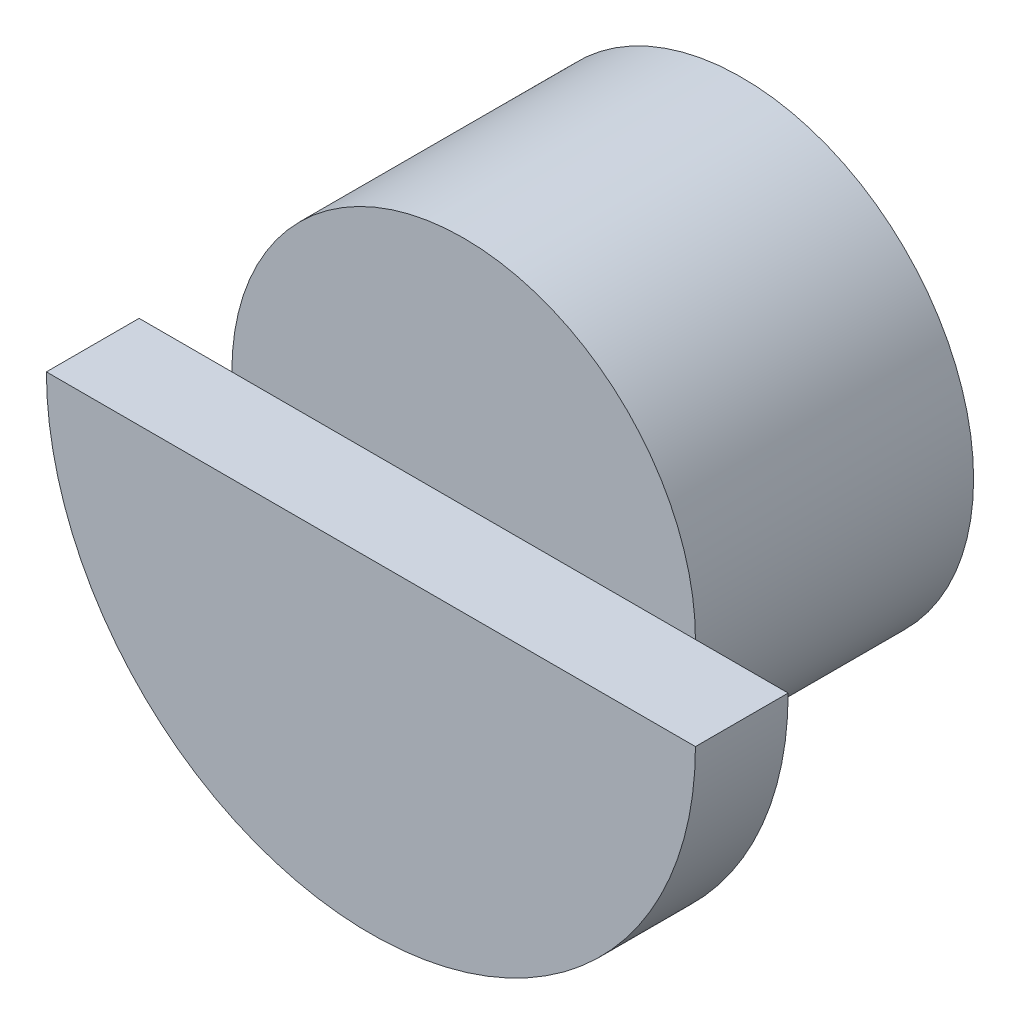
SolidWorks part; units mm, degrees
ref_plane "Front Plane" through (0, 0, 0) normal (0, 0, 1) x (1, 0, 0)
ref_plane "Top Plane" through (0, 0, 0) normal (0, 1, 0) x (1, 0, 0)
ref_plane "Right Plane" through (0, 0, 0) normal (1, 0, 0) x (0, 0, -1)
sketch "Sketch1" plane through (0, 0, 0) normal (0, 0, 1) x (1, 0, 0)
  circle A0 centre (0, 0) radius 25
  dimension "D1" = 50
extrude "Boss-Extrude1" add sketch "Sketch1" along normal blind 30
sketch "Sketch2" plane through (0, 0, 30) normal (0, 0, 1) x (1, 0, 0)
  line L0 (-35, 0) -> (35, 0)
  arc A0 (-35, 0) -> (35, 0) centre (0, 0) ccw
  dimension "D1" = 70
extrude "Boss-Extrude2" add sketch "Sketch2" along normal blind 10
